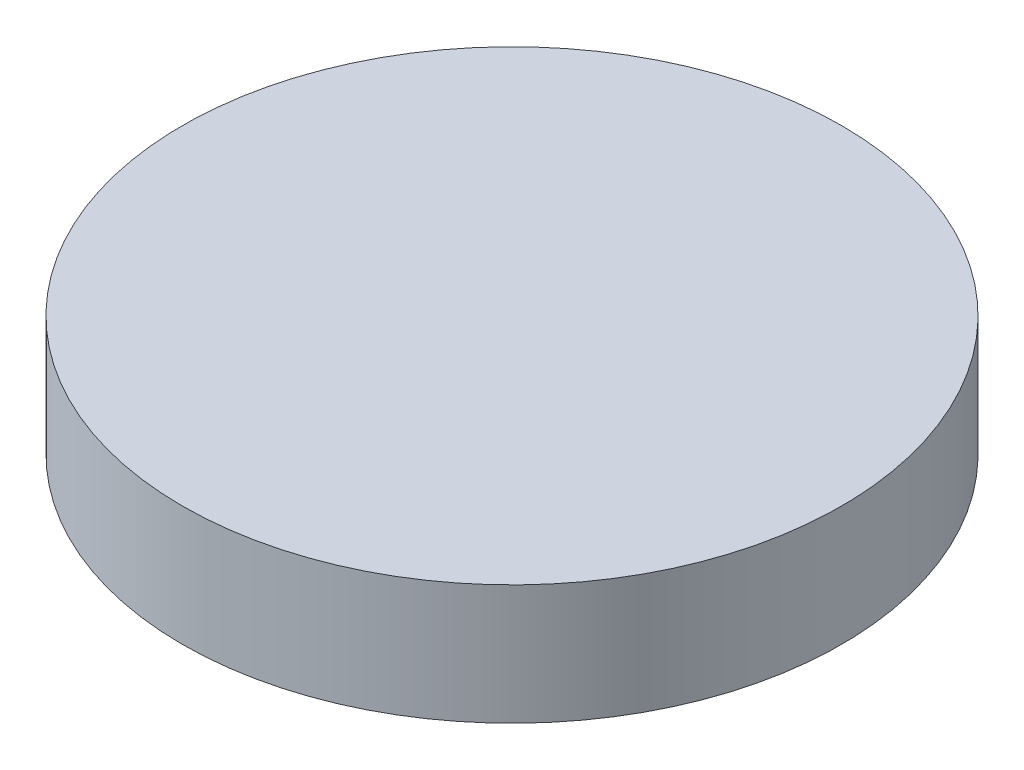
SolidWorks part; units mm, degrees
ref_plane "Front Plane" through (0, 0, 0) normal (0, 0, 1) x (1, 0, 0)
ref_plane "Top Plane" through (0, 0, 0) normal (0, 1, 0) x (1, 0, 0)
ref_plane "Right Plane" through (0, 0, 0) normal (1, 0, 0) x (0, 0, -1)
sketch "Sketch1" plane through (0, 0, 0) normal (0, 1, 0) x (1, 0, 0)
  circle A0 centre (0, 0) radius 110
  dimension "D1" = 220
extrude "Extrude1" add sketch "Sketch1" along normal blind 40
